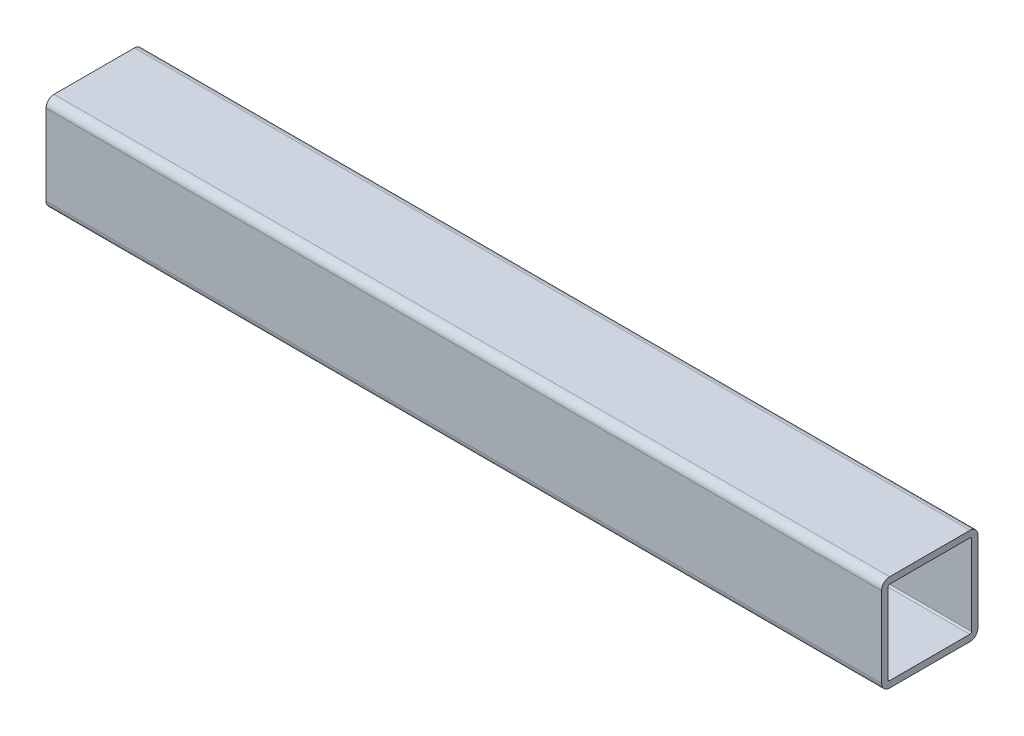
SolidWorks part; units mm, degrees
ref_plane "Front Plane" through (0, 0, 0) normal (0, 0, 1) x (1, 0, 0)
ref_plane "Top Plane" through (0, 0, 0) normal (0, 1, 0) x (1, 0, 0)
ref_plane "Right Plane" through (0, 0, 0) normal (1, 0, 0) x (0, 0, -1)
sketch "Sketch1" plane through (0, 0, 0) normal (1, 0, 0) x (0, 0, -1)
  line L1 (-15.875, 19.05) -> (15.875, 19.05)
  line L2 (-19.05, 15.875) -> (-19.05, -15.875)
  line L3 (-15.875, -19.05) -> (15.875, -19.05)
  line L4 (19.05, 15.875) -> (19.05, -15.875)
  line L5 (-19.05, 19.05) -> (19.05, -19.05) construction
  line L6 (-19.05, -19.05) -> (19.05, 19.05) construction
  arc A0 (-19.05, -15.875) -> (-15.875, -19.05) centre (-15.875, -15.875) ccw
  arc A1 (15.875, -19.05) -> (19.05, -15.875) centre (15.875, -15.875) ccw
  arc A2 (19.05, 15.875) -> (15.875, 19.05) centre (15.875, 15.875) ccw
  arc A3 (-15.875, 19.05) -> (-19.05, 15.875) centre (-15.875, 15.875) ccw
  point P0 (0, 0)
  dimension "D3" = 3.175
  dimension "D1" = 38.1
  dimension "D2" = 38.1
extrude "Extrude-Thin1" add sketch "Sketch1" along normal mid plane 330.2 thin
sketch "Sketch7" plane through (165.1, 0, 0) normal (1, 0, 0) x (0, 0, -1)
  line L0 (16.51, 0) -> (-16.51, 0) construction
  line L1 (16.51, -15.875) -> (16.51, 15.875) construction
  line L2 (-16.51, 15.875) -> (-16.51, -15.875) construction
  line L3 (0, 16.51) -> (0, -16.51) construction
  line L4 (15.875, 16.51) -> (-15.875, 16.51) construction
  line L5 (-15.875, -16.51) -> (15.875, -16.51) construction
sketch "Sketch9" plane through (-165.1, 0, 0) normal (-1, 0, 0) x (0, 0, 1)
  line L0 (0, 16.51) -> (0, -16.51) construction
  line L1 (-15.875, 16.51) -> (15.875, 16.51) construction
  line L2 (15.875, -16.51) -> (-15.875, -16.51) construction
  line L3 (16.51, 0) -> (-16.51, 0) construction
  line L4 (16.51, 15.875) -> (16.51, -15.875) construction
  line L5 (-16.51, -15.875) -> (-16.51, 15.875) construction
